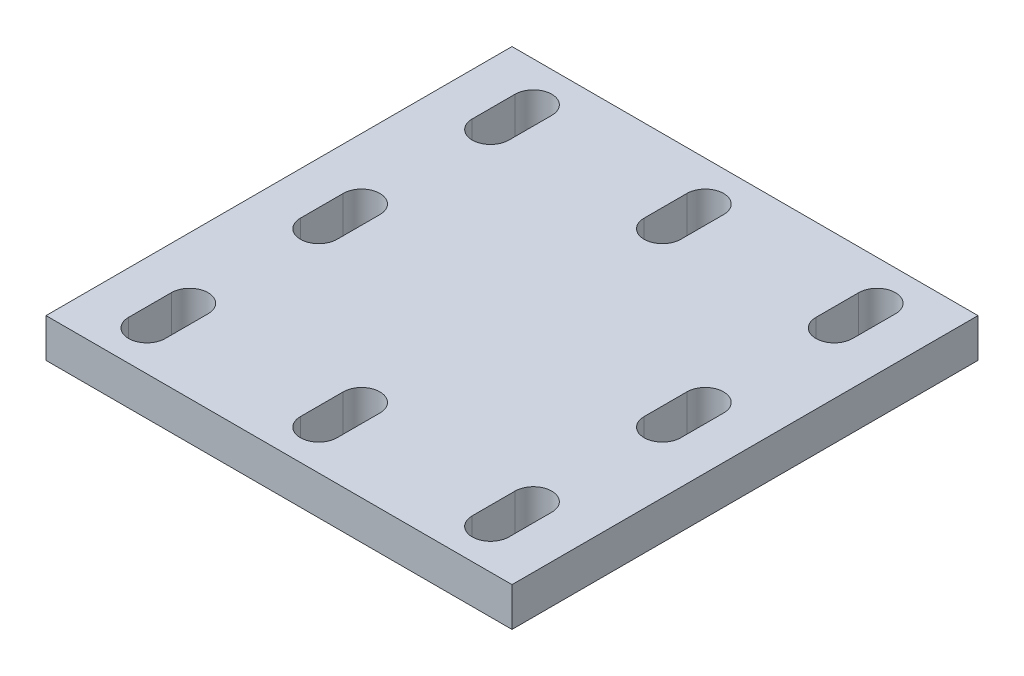
SolidWorks part; units mm, degrees
material "ABS_rapid_prototype"
ref_plane "Front" through (0, 0, 0) normal (0, 0, 1) x (1, 0, 0)
ref_plane "Top" through (0, 0, 0) normal (0, 1, 0) x (1, 0, 0)
ref_plane "Right" through (0, 0, 0) normal (1, 0, 0) x (0, 0, -1)
sketch "Sketch1" plane through (0, 0, 0) normal (0, 1, 0) x (1, 0, 0)
  line L1 (-38.1, 38.1) -> (38.1, 38.1)
  line L2 (-38.1, 38.1) -> (-38.1, -38.1)
  line L3 (-38.1, -38.1) -> (38.1, -38.1)
  line L4 (38.1, 38.1) -> (38.1, -38.1)
  line L5 (-38.1, 38.1) -> (38.1, -38.1) construction
  line L6 (-38.1, -38.1) -> (38.1, 38.1) construction
  point P0 (0, 0)
  dimension "D1" = 76.2
extrude "Boss-Extrude1" add sketch "Sketch1" along normal blind 6.35
sketch "Sketch2" plane through (0, 0, 0) normal (0, -1, 0) x (1, 0, 0)
  circle A0 centre (0, 0) radius 1.5875
  circle A1 centre (0, 0) radius 3
  dimension "D1" = 3.175
  dimension "D2" = 6
extrude "Boss-Extrude2" add sketch "Sketch2" along normal blind 10 contours A1
sketch "Sketch3" plane through (0, -10, 0) normal (0, -1, 0) x (1, 0, 0)
  circle A0 centre (0, 0) radius 1.5875
  dimension "D1" = 3.175
extrude "Cut-Extrude1" cut sketch "Sketch3" against normal blind 10
sketch "Sketch5" plane through (0, 6.35, 0) normal (0, 1, 0) x (1, 0, 0)
  line L0 (-28.1, 31.6) -> (-28.1, 24.6) construction
  line L1 (38.1, 38.1) -> (-38.1, 38.1) construction
  line L2 (-25.1, 31.6) -> (-25.1, 24.6)
  line L3 (-31.1, 31.6) -> (-31.1, 24.6)
  line L4 (-38.1, 38.1) -> (-38.1, -38.1) construction
  line L5 (-3, 31.6) -> (-3, 24.6)
  line L6 (3, 31.6) -> (3, 24.6)
  line L7 (0, 31.6) -> (0, 24.6) construction
  line L8 (25.1, 31.6) -> (25.1, 24.6)
  line L9 (31.1, 31.6) -> (31.1, 24.6)
  line L10 (28.1, 31.6) -> (28.1, 24.6) construction
  line L14 (25.1, 3.5) -> (25.1, -3.5)
  line L15 (31.1, 3.5) -> (31.1, -3.5)
  line L16 (28.1, 3.5) -> (28.1, -3.5) construction
  line L17 (-3, -24.6) -> (-3, -31.6)
  line L18 (3, -24.6) -> (3, -31.6)
  line L19 (0, -24.6) -> (0, -31.6) construction
  line L20 (25.1, -24.6) -> (25.1, -31.6)
  line L21 (31.1, -24.6) -> (31.1, -31.6)
  line L22 (28.1, -24.6) -> (28.1, -31.6) construction
  line L23 (-31.1, 3.5) -> (-31.1, -3.5)
  line L24 (-25.1, 3.5) -> (-25.1, -3.5)
  line L25 (-28.1, 3.5) -> (-28.1, -3.5) construction
  line L26 (-31.1, -24.6) -> (-31.1, -31.6)
  line L27 (-25.1, -24.6) -> (-25.1, -31.6)
  line L28 (-28.1, -24.6) -> (-28.1, -31.6) construction
  line L29 (3, 3.5) -> (3, -3.5) [skipped]
  line L30 (-3, 3.5) -> (-3, -3.5) [skipped]
  arc A0 (-25.1, 31.6) -> (-31.1, 31.6) centre (-28.1, 31.6) ccw
  arc A1 (-31.1, 24.6) -> (-25.1, 24.6) centre (-28.1, 24.6) ccw
  arc A2 (3, 31.6) -> (-3, 31.6) centre (0, 31.6) ccw
  arc A3 (-3, 24.6) -> (3, 24.6) centre (0, 24.6) ccw
  arc A4 (31.1, 31.6) -> (25.1, 31.6) centre (28.1, 31.6) ccw
  arc A5 (25.1, 24.6) -> (31.1, 24.6) centre (28.1, 24.6) ccw
  arc A8 (31.1, 3.5) -> (25.1, 3.5) centre (28.1, 3.5) ccw
  arc A9 (25.1, -3.5) -> (31.1, -3.5) centre (28.1, -3.5) ccw
  arc A10 (3, -24.6) -> (-3, -24.6) centre (0, -24.6) ccw
  arc A11 (-3, -31.6) -> (3, -31.6) centre (0, -31.6) ccw
  arc A12 (31.1, -24.6) -> (25.1, -24.6) centre (28.1, -24.6) ccw
  arc A13 (25.1, -31.6) -> (31.1, -31.6) centre (28.1, -31.6) ccw
  arc A14 (-25.1, 3.5) -> (-31.1, 3.5) centre (-28.1, 3.5) ccw
  arc A15 (-31.1, -3.5) -> (-25.1, -3.5) centre (-28.1, -3.5) ccw
  arc A16 (-25.1, -24.6) -> (-31.1, -24.6) centre (-28.1, -24.6) ccw
  arc A17 (-31.1, -31.6) -> (-25.1, -31.6) centre (-28.1, -31.6) ccw
  arc A18 (3, 3.5) -> (-3, 3.5) centre (0, 3.5) ccw [skipped]
  arc A19 (-3, -3.5) -> (3, -3.5) centre (0, -3.5) ccw [skipped]
  point P4 (-28.1, 28.1)
  point P15 (0, 28.1)
  point P22 (28.1, 28.1)
  point P29 (0, 0)
  point P36 (28.1, 0)
  point P43 (0, -28.1)
  point P50 (28.1, -28.1)
  point P57 (-28.1, 0)
  point P64 (-28.1, -28.1)
  dimension "D1" = 10
  dimension "D2" = 10
  dimension "D3" = 3
  dimension "D4" = 3
extrude "Cut-Extrude2" cut sketch "Sketch5" against normal through all
